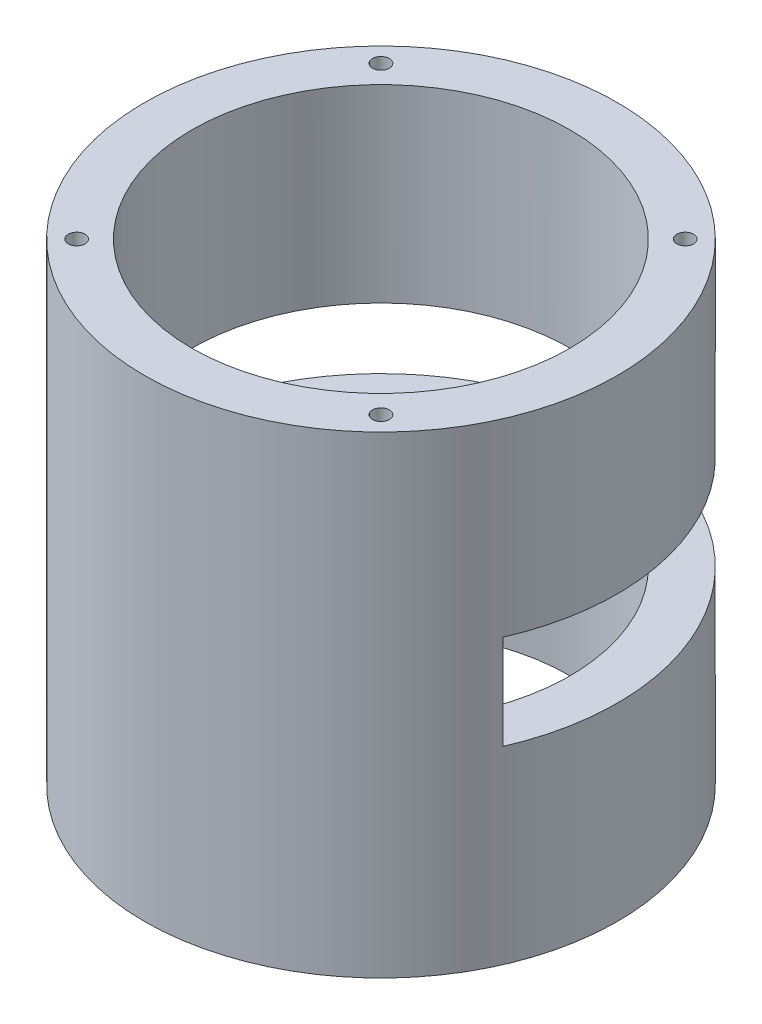
SolidWorks part; units mm, degrees
ref_plane "Front Plane" through (0, 0, 0) normal (0, 0, 1) x (1, 0, 0)
ref_plane "Top Plane" through (0, 0, 0) normal (0, 1, 0) x (1, 0, 0)
ref_plane "Right Plane" through (0, 0, 0) normal (1, 0, 0) x (0, 0, -1)
sketch "Sketch1" plane through (0, 0, 0) normal (0, 1, 0) x (1, 0, 0)
  circle A0 centre (0, 0) radius 25.4
  circle A1 centre (0, 0) radius 31.75
  dimension "D1" = 50.8
  dimension "D2" = 63.5
extrude "Boss-Extrude1" add sketch "Sketch1" along normal blind 63.5
hole_wizard "#4-40 Tapped Hole1" positions "Sketch3" profile "Sketch2" tap size "#4-40" standard "ANSI Inch"
sketch "Sketch3" plane through (0, 0, 0) normal (0, -1, 0) x (-1, 0, 0)
  line L0 (-20.4301, -20.4301) -> (20.4301, 20.4301) construction
  line L2 (20.4301, -20.4301) -> (-20.4301, 20.4301) construction
  line L4 (0, 0) -> (0, -22.8191) construction
  circle A0 centre (0, 0) radius 28.8925 construction
  point P0 (20.4301, -20.4301)
  point P2 (-20.4301, -20.4301)
  point P4 (-20.4301, 20.4301)
  point P6 (20.4301, 20.4301)
  dimension "D1" = 57.785
  dimension "D2" = 90
  dimension "D3" = 45
sketch "Sketch2" plane through (-20.4301, 0, 20.4301) normal (1, 0, 0) x (0, 0, -1)
  line L0 (0, 0) -> (0, 8.2992)
  line L1 (0, 8.2992) -> (1.1303, 7.62)
  line L2 (1.1303, 7.62) -> (1.1303, 0)
  line L5 (1.1303, 0) -> (0, 0)
  line L10 (0, 8.2992) -> (-1.1303, 7.62) construction
  line L11 (0, -6.35) -> (0, 107.95) construction
  dimension "Tap Drill Dia." = 2.2606
  dimension "Tap Drill Depth" = 7.62
  dimension "Drill Angle" = 118
ref_plane "Plane1" through (0, 25.4, 0) normal (0, 1, 0) x (1, 0, 0)
sketch "Sketch4" plane through (0, 25.4, 0) normal (0, 1, 0) x (1, 0, 0)
  line L0 (-54.714, -12.7) -> (57.9563, -12.7)
  line L1 (57.9563, -12.7) -> (57.9563, 43.7471)
  line L2 (57.9563, 43.7471) -> (-54.714, 43.7471)
  line L3 (-54.714, 43.7471) -> (-54.714, -12.7)
  dimension "D1" = 12.7
extrude "Cut-Extrude1" cut sketch "Sketch4" along normal blind 12.7
ref_plane "Plane2" through (0, 31.75, 0) normal (0, 1, 0) x (1, 0, 0)
mirror "Mirror1" about plane through (0, 31.75, 0) normal (0, 1, 0) of "#4-40 Tapped Hole1"
